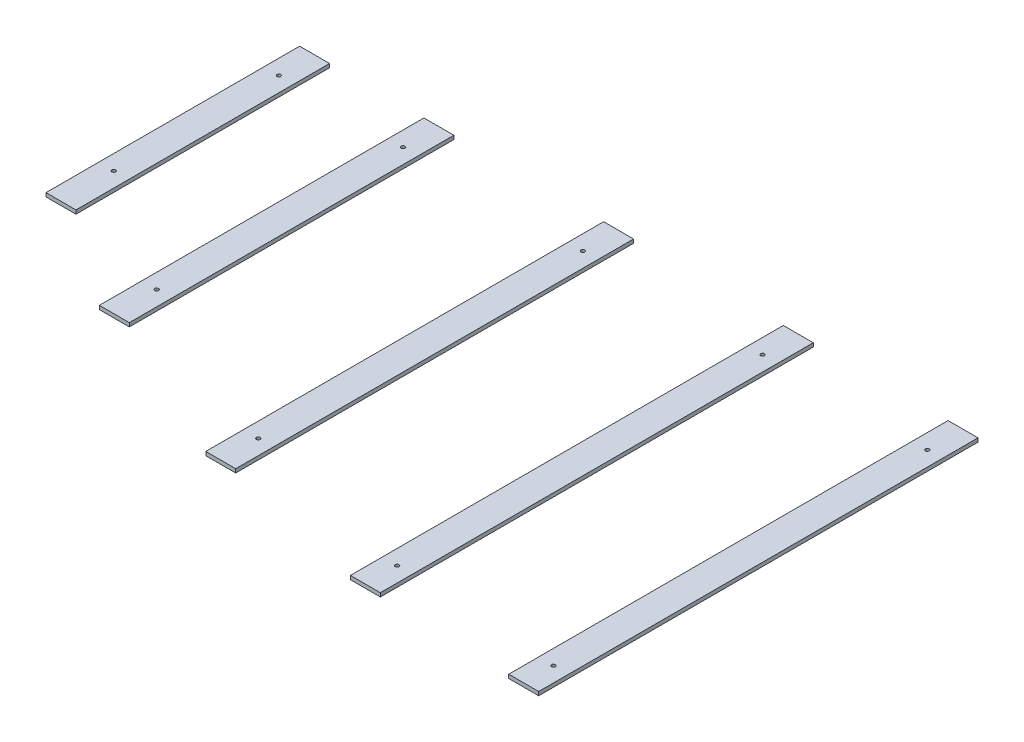
SolidWorks part; units mm, degrees
ref_plane "Front Plane" through (0, 0, 0) normal (0, 0, 1) x (1, 0, 0)
ref_plane "Top Plane" through (0, 0, 0) normal (0, 1, 0) x (1, 0, 0)
ref_plane "Right Plane" through (0, 0, 0) normal (1, 0, 0) x (0, 0, -1)
sketch "Sketch4" plane through (0, 0, 0) normal (0, 1, 0) x (1, 0, 0)
  line L4 (23232.9446, -10111.0305) -> (23232.9446, -10251.0305) construction
  line L5 (23232.9446, -9942.5829) -> (23032.9446, -9942.5829)
  line L6 (23232.9446, -9942.5829) -> (23232.9446, -12876.1567)
  line L7 (23232.9446, -12876.1567) -> (23032.9446, -12876.1567)
  line L8 (23032.9446, -9942.5829) -> (23032.9446, -12876.1567)
  line L9 (22132.9446, -9942.5829) -> (21932.9446, -9942.5829)
  line L10 (22132.9446, -9942.5829) -> (22132.9446, -12833.5838)
  line L11 (22132.9446, -12833.5838) -> (21932.9446, -12833.5838)
  line L12 (21932.9446, -9942.5829) -> (21932.9446, -12833.5838)
  line L13 (20932.9446, -9942.5829) -> (20732.9446, -9942.5829)
  line L14 (20932.9446, -9942.5829) -> (20932.9446, -12599.4325)
  line L15 (20932.9446, -12599.4325) -> (20732.9446, -12599.4325)
  line L16 (20732.9446, -9942.5829) -> (20732.9446, -12599.4325)
  line L17 (19732.9446, -9942.5829) -> (19532.9446, -9942.5829)
  line L18 (19732.9446, -9942.5829) -> (19732.9446, -12109.8436)
  line L19 (19732.9446, -12109.8436) -> (19532.9446, -12109.8436)
  line L20 (19532.9446, -9942.5829) -> (19532.9446, -12109.8436)
  line L21 (18902.9446, -9942.5829) -> (18702.9446, -9942.5829)
  line L22 (18902.9446, -9942.5829) -> (18902.9446, -11636.2195)
  line L23 (18902.9446, -11636.2195) -> (18702.9446, -11636.2195)
  line L24 (18702.9446, -9942.5829) -> (18702.9446, -11636.2195)
  line L25 (18702.9446, -10111.0305) -> (18702.9446, -10251.0305) construction
  line L26 (23132.9446, -12748.1199) -> (23132.9446, -12608.0593) construction
  line L27 (22032.9446, -12550.6075) -> (22032.9446, -12691.8491) construction
  line L28 (20832.9446, -12422.3488) -> (20832.9446, -12275.1597) construction
  line L29 (19632.9446, -11906.9658) -> (19632.9446, -11746.8651) construction
  line L30 (18802.9446, -11371.765) -> (18802.9446, -11195.5746) construction
  line L31 (23132.9446, -10251.0305) -> (23132.9446, -10111.0305) construction
  line L32 (18702.9446, -10251.0305) -> (23232.9446, -10251.0305) construction
  line L33 (23232.9446, -10111.0305) -> (18702.9446, -10111.0305) construction
  circle A0 centre (23132.9446, -12678.0896) radius 12.5
  arc A1 (18702.9446, -11295.1434) -> (23232.9446, -12744.4799) centre (22932.9446, -5878.0705) ccw construction
  arc A2 (18702.9446, -11116.3765) -> (23232.9446, -12604.3436) centre (22932.9446, -5878.0705) ccw construction
  circle A3 centre (22032.9446, -12621.2283) radius 12.5
  circle A4 centre (20832.9446, -12348.7542) radius 12.5
  circle A5 centre (19632.9446, -11826.9154) radius 12.5
  circle A6 centre (18802.9446, -11283.6698) radius 12.5
  circle A7 centre (18802.9446, -10181.0305) radius 12.5
  circle A8 centre (19632.9446, -10181.0305) radius 12.5
  circle A9 centre (20832.9446, -10181.0305) radius 12.5
  circle A10 centre (22032.9446, -10181.0305) radius 12.5
  circle A11 centre (23132.9446, -10181.0305) radius 12.5
  arc A12 (18702.9446, -11116.3765) -> (23232.9446, -12604.3436) centre (22932.9446, -5878.0705) ccw construction
  point P22 (23132.9446, -9942.5829)
  point P23 (22032.9446, -9942.5829)
  point P24 (20832.9446, -9942.5829)
  point P25 (19632.9446, -9942.5829)
  point P26 (23132.9446, -12876.1567)
  point P30 (20832.9446, -12599.4325)
  point P40 (23132.9446, -12678.0896)
  point P59 (22032.9446, -12621.2283)
  point P60 (22032.9446, -12833.5838)
  point P68 (20832.9446, -12348.7542)
  point P69 (19632.9446, -12109.8436)
  point P73 (19632.9446, -11826.9154)
  point P74 (18802.9446, -11283.6698)
  point P75 (18802.9446, -11636.2195)
  point P78 (23132.9446, -10181.0305)
  point P91 (18802.9446, -9942.5829)
  dimension "D5" = 25
  dimension "D1" = 200
  dimension "D2" = 1200
  dimension "D3" = 1200
  dimension "D4" = 1200
  dimension "D6" = 100
  dimension "D7" = 70
extrude "Boss-Extrude1" add sketch "Sketch4" along normal blind 25
